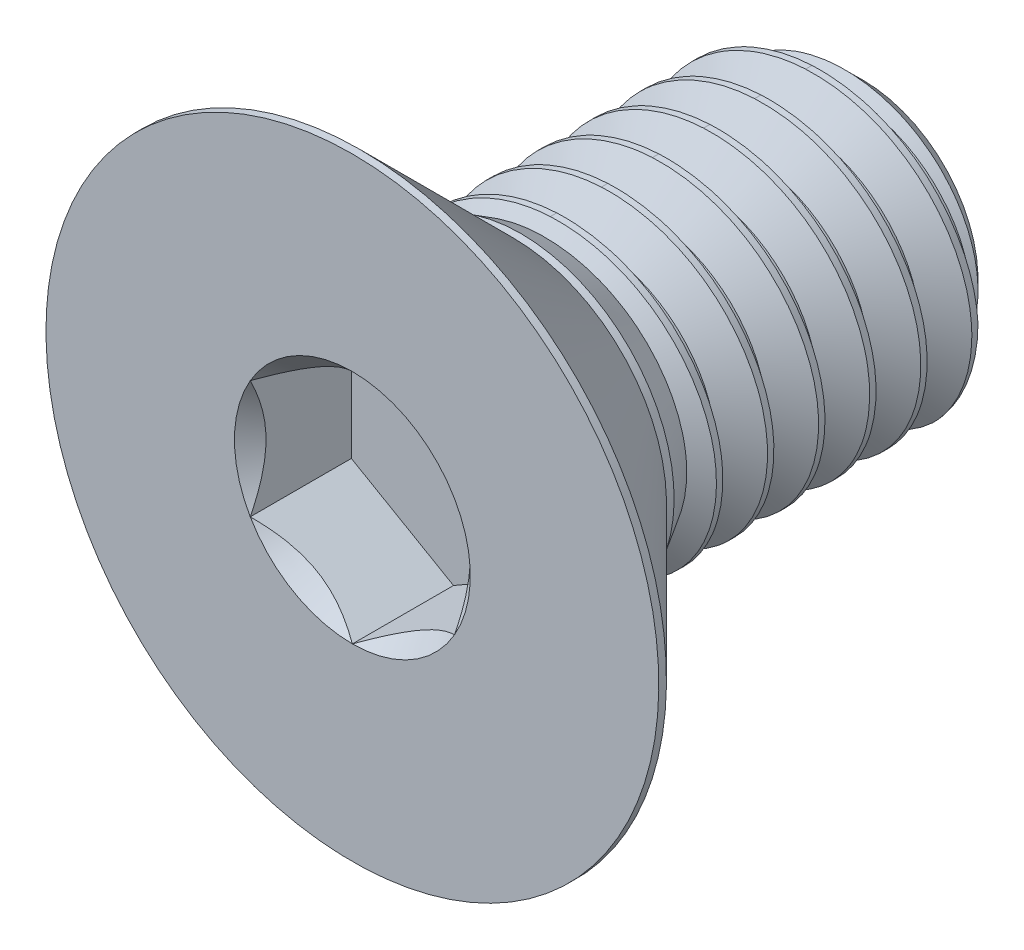
SolidWorks part; units mm, degrees
material "AISI 316 Annealed Stainless Steel Bar (SS)"
ref_plane "Front" through (0, 0, 0) normal (0, 0, 1) x (1, 0, 0)
ref_plane "Top" through (0, 0, 0) normal (0, 1, 0) x (1, 0, 0)
ref_plane "Right" through (0, 0, 0) normal (1, 0, 0) x (0, 0, -1)
sketch "Sketch1" plane through (0, 0, 0) normal (0, 0, 1) x (1, 0, 0)
  line L1 (2, 1.1547) -> (0, 2.3094)
  line L8 (0, 2.3094) -> (-2, 1.1547)
  line L9 (-2, 1.1547) -> (-2, -1.1547)
  line L10 (-2, -1.1547) -> (0, -2.3094)
  line L11 (0, -2.3094) -> (2, -1.1547)
  line L12 (2, -1.1547) -> (2, 1.1547)
  circle A0 centre (0, 0) radius 2 construction
  circle A1 centre (0, 0) radius 6
  point P7 (0, 6)
  dimension "Head Dia" = 12
  dimension "Hex" = 4
sketch "Sketch2" plane through (0, 0, 0) normal (1, 0, 0) x (0, 0, -1)
  line L2 (0, 0) -> (6.7, 0) construction
  line L3 (6.7, 0) -> (6.7, 3)
  line L6 (6.7, 3) -> (0, 3)
  line L8 (0, 3) -> (-0.15, 3)
  line L9 (-0.15, 3) -> (-3.15, 6)
  line L11 (-3.15, 6) -> (-3.3, 6)
  line L13 (-3.3, 6) -> (-3.3, 0)
  line L14 (-3.3, 0) -> (0, 0) construction
  line L15 (6.6375, 3.1083) -> (7.1375, 2.2422) construction
  line L16 (7.1375, 2.2422) -> (7.6375, 3.1083) construction
  line L17 (7.6375, 3.1083) -> (6.6375, 3.1083) construction
  line L18 (6.6688, 3.0541) -> (7.6063, 3.0541)
  line L19 (7.6063, 3.0541) -> (7.2, 2.3505)
  line L20 (7.2, 2.3505) -> (7.075, 2.3505)
  line L21 (7.075, 2.3505) -> (6.6688, 3.0541)
  line L22 (7.1375, 2.3505) -> (7.1375, 2.2422) construction
  line L23 (6.7, 3) -> (7.575, 3) construction
  line L24 (7.1375, 3.1083) -> (7.1375, 3) construction
  line L25 (6.7, 2.25) -> (5.95, 3)
  line L26 (6.7, -3) -> (0, -3)
  point P28 (7.1375, 3.0541)
  point P32 (5.2, -3)
  point P33 (-1.32, 0)
  point P35 (-3.3, 6)
  dimension "Dia" = 6
  dimension "Head Ht" = 3.3
  dimension "D2" = 45
  dimension "Lg" = 10
  dimension "Pitch" = 1
  dimension "D3" = 0.125
  dimension "D1" = 45
  dimension "D4" = 0.75
  dimension "D5" = 1.5
  dimension "D6" = 1.98
sketch "Sketch7" plane through (0, 0, 0) normal (1, 0, 0) x (0, 0, -1)
  line L2 (-3.3, 0) -> (-3.3, 6)
  line L3 (-3.3, 6) -> (-3.15, 6)
  line L5 (-3.15, 6) -> (-0.15, 3)
  line L6 (-0.15, 3) -> (5.95, 3)
  line L8 (5.95, 3) -> (6.7, 2.25)
  line L9 (6.7, 2.25) -> (6.7, 0)
  line L11 (6.7, 0) -> (-3.3, 0)
revolve "Revolve2" add sketch "Sketch7" angle 360 mid plane about L11
sketch "Sketch5" plane through (0, 0, 3.3) normal (0, 0, 1) x (1, 0, 0)
  line L0 (2, -1.1547) -> (2, 1.1547) construction
  line L1 (0, -2.3094) -> (2, -1.1547) construction
  line L2 (-2, -1.1547) -> (0, -2.3094) construction
  line L3 (-2, 1.1547) -> (-2, -1.1547) construction
  line L4 (0, 2.3094) -> (-2, 1.1547) construction
  line L5 (2, 1.1547) -> (0, 2.3094) construction
  line L6 (2, -1.1547) -> (2, 1.1547)
  line L7 (0, -2.3094) -> (2, -1.1547)
  line L8 (-2, -1.1547) -> (0, -2.3094)
  line L9 (-2, 1.1547) -> (-2, -1.1547)
  line L10 (0, 2.3094) -> (-2, 1.1547)
  line L11 (2, 1.1547) -> (0, 2.3094)
extrude "Cut-Extrude2" cut sketch "Sketch5" against normal up to vertex (1.98 mm away) up to point (0, 0, 1.32)
sketch "Sketch6" plane through (0, 0, 3.3) normal (0, 0, 1) x (1, 0, 0)
  circle A0 centre (0, 0) radius 2.3094
extrude "Cut-Extrude3" cut sketch "Sketch6" against normal up to vertex (1.98 mm away) draft 45 up to point (0, 0, 1.32)
sketch "Sketch3" plane through (0, 0, -6.7) normal (0, 0, -1) x (-1, 0, 0)
  circle A0 centre (0, 0) radius 3
split "Split1" trim tools "Front" bodies to split 113 resulting bodies 125 126
curve "Helix/Spiral1" pitch 1 height 7.7 turns 7.7
sketch "Sketch8" plane through (0, 0, 0) normal (1, 0, 0) x (0, 0, -1)
  line L0 (6.6688, 3.0541) -> (7.6063, 3.0541) construction
  line L1 (7.075, 2.3505) -> (6.6688, 3.0541) construction
  line L2 (7.2, 2.3505) -> (7.075, 2.3505) construction
  line L3 (7.6063, 3.0541) -> (7.2, 2.3505) construction
  line L4 (6.6688, 3.0541) -> (7.6063, 3.0541)
  line L5 (7.075, 2.3505) -> (6.6688, 3.0541)
  line L6 (7.2, 2.3505) -> (7.075, 2.3505)
  line L7 (7.6063, 3.0541) -> (7.2, 2.3505)
sweep "Cut-Sweep1" cut profiles "Sketch8" path "Helix/Spiral1"
sketch "Sketch9" plane through (0, 0, 0) normal (0, 0, 1) x (1, 0, 0)
  circle A0 centre (0, 0) radius 3
extrude "Boss-Extrude1" add sketch "Sketch9" against normal up to vertex (6.7 mm away) draft 30.9 up to point (0, 0, -6.7)
equation "\"D3@Helix/Spiral1\" =  ( \"Lg@Sketch2\" - \"Head Ht@Sketch2\" )  + \"Pitch@Sketch2\""
equation "\"D1\"= \"Head Ht@Sketch2\" * .7"
equation "\"D1\"= \"D1\""
equation "\"D4@Helix/Spiral1\" = \"Pitch@Sketch2\""
equation "\"D3@Sketch2\" = \"Pitch@Sketch2\" / 8"
equation "\"D4@Sketch2\" = \"Pitch@Sketch2\" * 0.75"
equation "\"D5@Sketch2\" = \"Pitch@Sketch2\" * 1.5"
equation "\"D6@Sketch2\" = \"Head Ht@Sketch2\" * 0.6"
